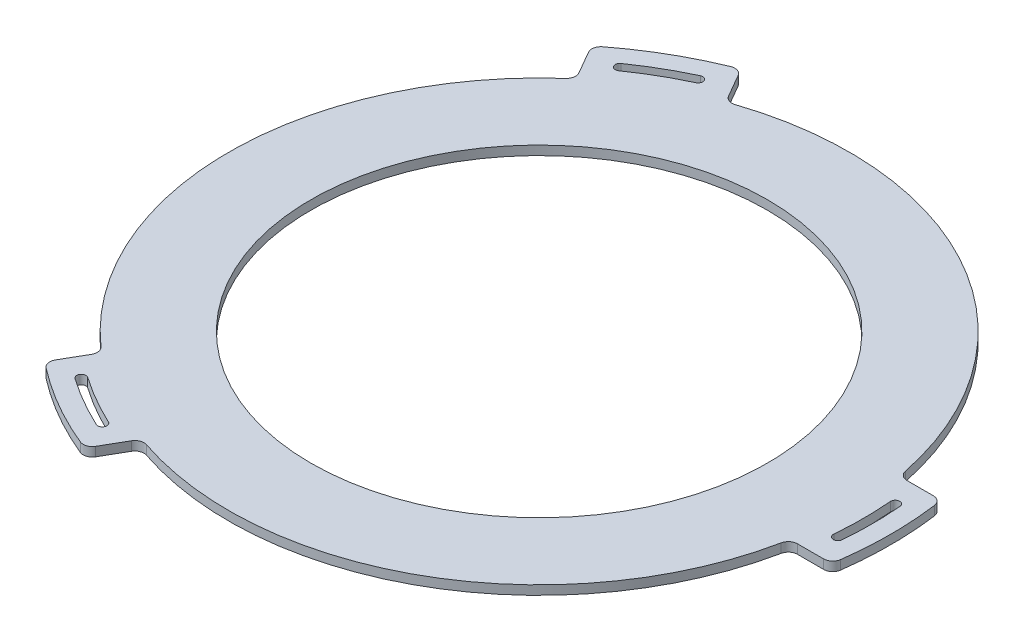
SolidWorks part; units mm, degrees
ref_plane "Front Plane" through (0, 0, 0) normal (0, 0, 1) x (1, 0, 0)
ref_plane "Top Plane" through (0, 0, 0) normal (0, 1, 0) x (1, 0, 0)
ref_plane "Right Plane" through (0, 0, 0) normal (1, 0, 0) x (0, 0, -1)
sketch "Sketch1" plane through (0, 0, 0) normal (0, 1, 0) x (1, 0, 0)
  circle A0 centre (0, 0) radius 250
  circle A1 centre (0, 0) radius 340
  circle A2 centre (0, 0) radius 250 construction
  arc A3 (-270.391, -206.1279) -> (-270.391, 206.1279) centre (0, 0) ccw construction
extrude "Boss-Extrude1" add sketch "Sketch1" along normal blind 10
sketch "Sketch2" plane through (0, 0, 0) normal (0, -1, 0) x (1, 0, 0)
  line L0 (0, 0) -> (540.2501, 0) construction
  line L1 (0, 0) -> (243.125, 421.1049) construction
  line L2 (371.6517, -60) -> (334.664, -60)
  line L3 (371.6517, 60) -> (334.664, 60)
  line L4 (363.6111, 31.8118) -> (353.6491, 30.9403) construction
  line L5 (-154.2557, 330.8023) -> (-150.0295, 321.7393) construction
  line L6 (-133.8643, 351.8598) -> (-115.3705, 319.8275)
  line L7 (-237.7874, 291.8598) -> (-219.2935, 259.8275)
  line L8 (-154.2557, -330.8023) -> (-150.0295, -321.7393) construction
  line L9 (-237.7874, -291.8598) -> (-219.2935, -259.8275)
  line L10 (-133.8643, -351.8598) -> (-115.3705, -319.8275)
  arc A0 (381.5624, 51.3333) -> (381.5624, -51.3333) centre (0, 0) cw
  circle A1 centre (0, 0) radius 340 construction
  arc A2 (371.6517, 60) -> (381.5624, 51.3333) centre (371.6517, 50) cw
  arc A3 (381.5624, -51.3333) -> (371.6517, -60) centre (371.6517, -50) cw
  arc A4 (363.6111, 31.8118) -> (363.6111, -31.8118) centre (0, 0) cw
  arc A5 (353.6491, -30.9403) -> (353.6491, 30.9403) centre (0, 0) ccw
  arc A6 (363.6111, 31.8118) -> (353.6491, 30.9403) centre (358.6301, 31.3761) ccw
  arc A7 (363.6111, -31.8118) -> (353.6491, -30.9403) centre (358.6301, -31.3761) cw
  arc A8 (-219.2935, 259.8275) -> (-115.3705, 319.8275) centre (0, 0) cw
  arc A9 (-209.3554, 298.9905) -> (-203.6196, 290.799) centre (-206.4875, 294.8947) ccw
  arc A10 (-154.2557, 330.8023) -> (-150.0295, 321.7393) centre (-152.1426, 326.2708) cw
  arc A11 (-203.6196, 290.799) -> (-150.0295, 321.7393) centre (0, 0) cw
  arc A12 (-154.2557, 330.8023) -> (-209.3554, 298.9905) centre (0, 0) ccw
  arc A13 (-235.2372, 304.7761) -> (-237.7874, 291.8598) centre (-229.1271, 296.8598) ccw
  arc A14 (-133.8643, 351.8598) -> (-146.3252, 356.1094) centre (-142.5246, 346.8598) ccw
  arc A15 (-146.3252, 356.1094) -> (-235.2372, 304.7761) centre (0, 0) ccw
  arc A16 (-146.3252, -356.1094) -> (-235.2372, -304.7761) centre (0, 0) cw
  arc A17 (-133.8643, -351.8598) -> (-146.3252, -356.1094) centre (-142.5246, -346.8598) cw
  arc A18 (-235.2372, -304.7761) -> (-237.7874, -291.8598) centre (-229.1271, -296.8598) cw
  arc A19 (-154.2557, -330.8023) -> (-209.3554, -298.9905) centre (0, 0) cw
  arc A20 (-203.6196, -290.799) -> (-150.0295, -321.7393) centre (0, 0) ccw
  arc A21 (-154.2557, -330.8023) -> (-150.0295, -321.7393) centre (-152.1426, -326.2708) ccw
  arc A22 (-209.3554, -298.9905) -> (-203.6196, -290.799) centre (-206.4875, -294.8947) cw
  arc A23 (-219.2935, -259.8275) -> (-115.3705, -319.8275) centre (0, 0) ccw
  arc A29 (334.664, -60) -> (334.664, 60) centre (0, 0) ccw
  point P12 (380.2959, 60)
  point P15 (380.2959, -60)
  point P36 (-242.1095, 299.3459)
  point P37 (-138.1864, 359.3459)
  point P52 (-138.1864, -359.3459)
  point P53 (-242.1095, -299.3459)
  dimension "D2" = 10
  dimension "D3" = 10
  dimension "D4" = 360
  dimension "D5" = 385
  dimension "D1" = 60
  dimension "D6" = 60
  dimension "D7" = 5
extrude "Boss-Extrude2" add sketch "Sketch2" against normal blind 10
fillet "Fillet1" radius 10 6 edges at (-219.2935, 5, -259.8275) (-115.3705, 5, -319.8275) (334.664, 5, -60) (334.664, 5, 60) (-115.3705, 5, 319.8275) (-219.2935, 5, 259.8275)
